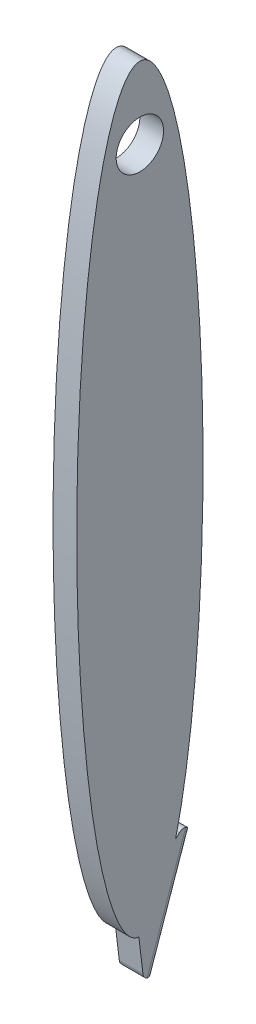
SolidWorks part; units mm, degrees
ref_plane "Front Plane" through (0, 0, 0) normal (0, 0, 1) x (1, 0, 0)
ref_plane "Top Plane" through (0, 0, 0) normal (0, 1, 0) x (1, 0, 0)
ref_plane "Right Plane" through (0, 0, 0) normal (1, 0, 0) x (0, 0, -1)
sketch "Sketch1" plane through (0, 0, 0) normal (1, 0, 0) x (0, 0, -1)
  ellipse E0 centre (0, 0) end of major axis (0, 76.2) minor radius 12.7
extrude "Boss-Extrude1" add sketch "Sketch1" along normal blind 4.7625
sketch "Sketch2" plane through (0, 0, 0) normal (1, 0, 0) x (0, 0, -1)
  line L3 (-0.9113, -70.3887) -> (1.2994, -88.5637)
  line L4 (1.2994, -88.5637) -> (11.6981, -58.5901)
  line L5 (-0.9113, -70.3887) -> (11.6981, -58.5901)
extrude "Boss-Extrude2" add sketch "Sketch2" along normal blind 4.7625
fillet "Fillet7" radius 1.27 4 edges at (2.3813, -88.5637, -1.2994) (4.7625, -73.5769, -6.4987) (2.3813, -58.5901, -11.6981) (0, -73.5769, -6.4987)
sketch "Sketch3" plane through (4.7625, 0, 0) normal (1, 0, 0) x (0, 0, -1)
  circle A0 centre (0, 61.7042) radius 4.7625
  point P2 (0, 61.7042)
extrude "Cut-Extrude1" cut sketch "Sketch3" against normal through all
